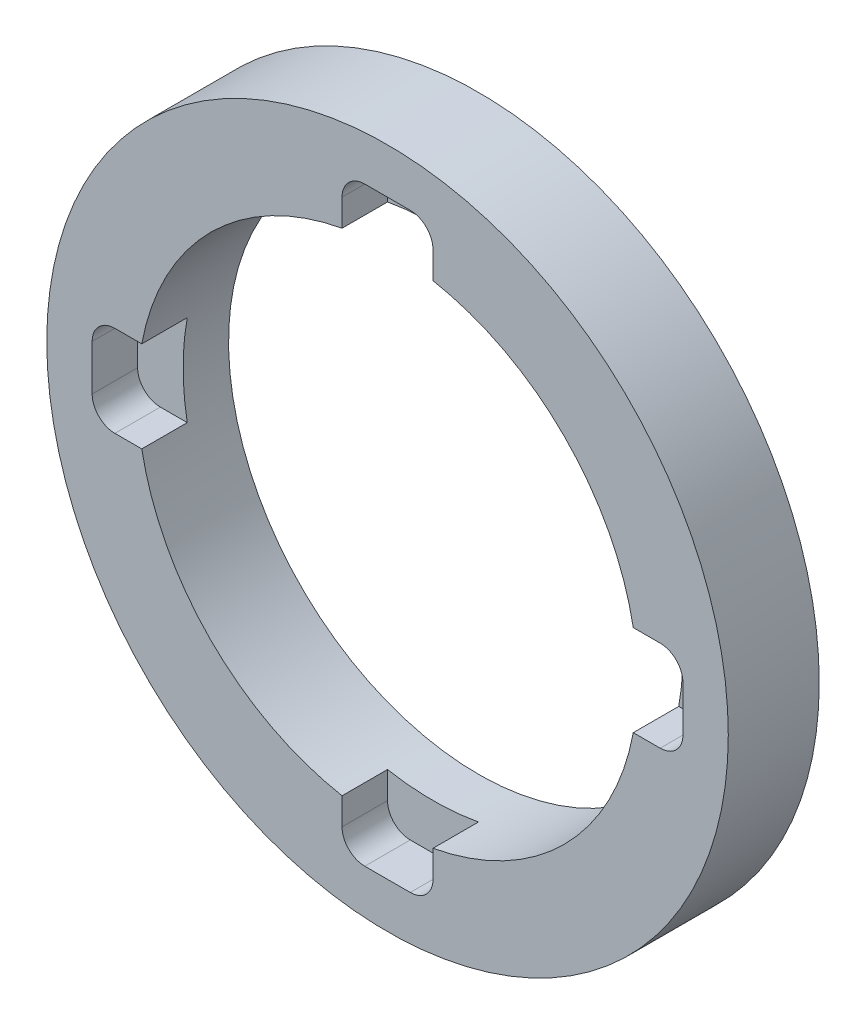
SolidWorks part; units mm, degrees
material "6061-T6 (SS)"
ref_plane "Front Plane" through (0, 0, 0) normal (0, 0, 1) x (1, 0, 0)
ref_plane "Top Plane" through (0, 0, 0) normal (0, 1, 0) x (1, 0, 0)
ref_plane "Right Plane" through (0, 0, 0) normal (1, 0, 0) x (0, 0, -1)
sketch "Sketch1" plane through (0, 0, 0) normal (0, 0, 1) x (1, 0, 0)
  circle A0 centre (0, 0) radius 47.5869
  circle A1 centre (0, 0) radius 34.8996
  dimension "D1" = 95.1738
  dimension "D2" = 69.7992
extrude "Boss-Extrude1" add sketch "Sketch1" along normal blind 12.7
sketch "Sketch2" plane through (0, 0, 12.7) normal (0, 0, 1) x (1, 0, 0)
  line L1 (-6.35, -41.2496) -> (6.35, -41.2496)
  line L2 (-6.35, -41.2496) -> (-6.35, 41.2496)
  line L3 (-6.35, 41.2496) -> (6.35, 41.2496)
  line L4 (6.35, -41.2496) -> (6.35, 41.2496)
  line L5 (-6.35, -41.2496) -> (6.35, 41.2496) construction
  line L6 (-6.35, 41.2496) -> (6.35, -41.2496) construction
  point P0 (0, 0)
  dimension "D1" = 12.7
  dimension "D2" = 82.4992
extrude "Cut-Extrude1" cut sketch "Sketch2" against normal blind 6.35
fillet "Fillet1" radius 3.175 4 edges at (-6.35, -41.2496, 9.525) (6.35, -41.2496, 9.525) (6.35, 41.2496, 9.525) (-6.35, 41.2496, 9.525)
pattern_circular "CirPattern1" count 2 over 90 about axis through (0, 0, 0) along (0, 0, 1) of "Cut-Extrude1", "Fillet1"
